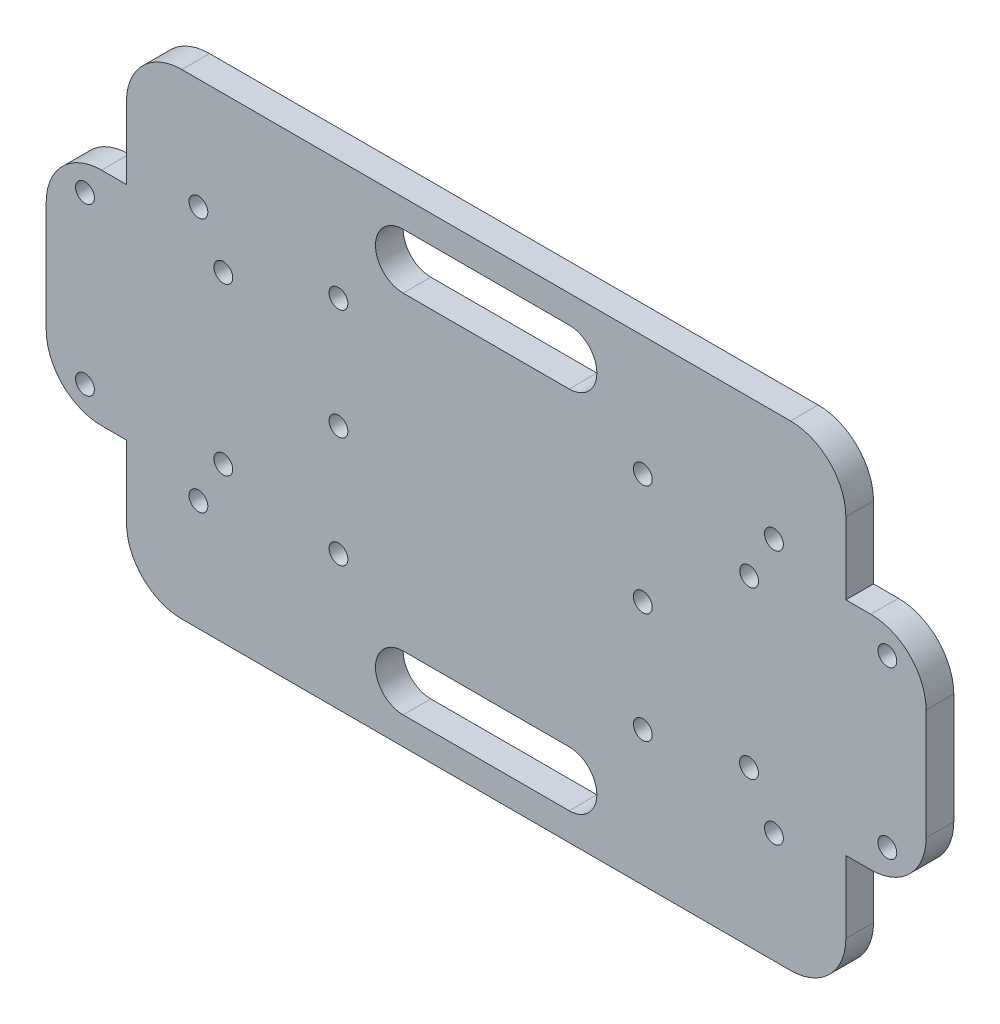
SolidWorks part; units mm, degrees
ref_plane "Front Plane" through (0, 0, 0) normal (0, 0, 1) x (1, 0, 0)
ref_plane "Top Plane" through (0, 0, 0) normal (0, 1, 0) x (1, 0, 0)
ref_plane "Right Plane" through (0, 0, 0) normal (1, 0, 0) x (0, 0, -1)
sketch "Sketch1" plane through (0, 0, 0) normal (0, 0, 1) x (1, 0, 0)
  line L0 (-65, -20) -> (-65, -33)
  line L1 (55, 43) -> (-55, 43)
  line L2 (65, 33) -> (65, 20)
  line L3 (55, -43) -> (-55, -43)
  line L4 (-65, 33) -> (-65, 20)
  line L5 (65, 43) -> (-65, -43) construction
  line L6 (65, -43) -> (-65, 43) construction
  line L7 (-65, 20) -> (-69.5, 20)
  line L9 (-65, -20) -> (-69.5, -20)
  line L10 (-79.5, 10) -> (-79.5, -10)
  line L11 (-65, 0) -> (-79.5, -20) construction
  line L12 (-65, 0) -> (-79.5, 20) construction
  line L13 (65, 20) -> (69.5, 20)
  line L15 (65, -20) -> (69.5, -20)
  line L16 (79.5, 10) -> (79.5, -10)
  line L17 (65, 0) -> (79.5, -20) construction
  line L18 (65, 0) -> (79.5, 20) construction
  line L19 (65, -20) -> (65, -33)
  arc A0 (-65, 33) -> (-55, 43) centre (-55, 33) cw
  arc A1 (-55, -43) -> (-65, -33) centre (-55, -33) cw
  arc A2 (55, -43) -> (65, -33) centre (55, -33) ccw
  arc A3 (65, 33) -> (55, 43) centre (55, 33) ccw
  arc A4 (-79.5, 10) -> (-69.5, 20) centre (-69.5, 10) cw
  arc A5 (-69.5, -20) -> (-79.5, -10) centre (-69.5, -10) cw
  arc A6 (79.5, 10) -> (69.5, 20) centre (69.5, 10) ccw
  arc A7 (69.5, -20) -> (79.5, -10) centre (69.5, -10) ccw
  point P0 (0, 0)
  point P18 (-65, 0)
  point P29 (65, 0)
  dimension "D3" = 10
  dimension "D4" = 10
  dimension "D5" = 10
  dimension "D6" = 10
  dimension "D8" = 10
  dimension "D9" = 10
  dimension "D11" = 10
  dimension "D12" = 10
  dimension "D1" = 130
  dimension "D2" = 86
  dimension "D7" = 40
  dimension "D10" = 40
extrude "Boss-Extrude2" add sketch "Sketch1" along normal blind 5
sketch "Sketch3" plane through (0, 0, 5) normal (0, 0, 1) x (1, 0, 0)
  line L0 (-79.5, 0) -> (-40.5, 0)
  line L1 (-79.5, 10) -> (-79.5, -10) construction
  line L2 (-40.5, 0) -> (-40.5, -20)
  line L3 (-40.5, -20) -> (-47.5, -20)
  line L4 (-47.5, -20) -> (-47.5, -15)
  line L5 (-40.5, 0) -> (-40.5, 20)
  line L6 (-40.5, 20) -> (-47.5, 20)
  line L7 (-47.5, 20) -> (-47.5, 15)
  line L8 (-47.5, -15) -> (-72.5, -15) construction
  line L9 (-47.5, 15) -> (-72.5, 15) construction
  line L10 (79.5, 0) -> (40.5, 0)
  line L11 (79.5, -10) -> (79.5, 10) construction
  line L12 (40.5, 0) -> (40.5, 20)
  line L13 (40.5, 20) -> (47.5237, 20)
  line L14 (47.5237, 20) -> (47.5237, 16.7)
  line L15 (40.5, 0) -> (40.5, -20)
  line L16 (40.5, -20) -> (47.5, -20)
  line L17 (47.5, -20) -> (47.5, -15)
  line L18 (47.5, -15) -> (72.5, -15)
  line L19 (49.2237, 15) -> (72.5, 15)
  line L20 (0, 43) -> (0, 33) construction
  line L21 (-39.1929, 31.3543) -> (-26.6929, 31.3543)
  line L25 (-39.1929, 31.3543) -> (39.1929, -31.3543) construction
  line L26 (-39.1929, -31.3543) -> (39.1929, 31.3543) construction
  line L27 (-26.6929, 31.3543) -> (-26.6929, 21.3543) construction
  line L28 (-26.6929, 21.3543) -> (-26.6929, 1.3543) construction
  line L29 (-26.6929, 1.3543) -> (-26.6929, -18.6457) construction
  line L30 (-26.6929, -18.6457) -> (28.3071, -18.6457) construction
  line L31 (28.3071, -18.6457) -> (28.3071, 1.3543) construction
  line L32 (28.3071, 1.3543) -> (28.3071, 21.3543) construction
  line L33 (47.5237, 43) -> (47.5237, 23) construction
  line L34 (55, 43) -> (-55, 43) construction
  line L35 (65, 23) -> (52, 23) construction
  line L37 (47.5, -43) -> (47.5, -23) construction
  line L38 (-55, -43) -> (55, -43) construction
  line L39 (65, -23) -> (52, -23) construction
  line L41 (-47.5, -43) -> (-47.5, -23) construction
  line L42 (-65, -23) -> (-52, -23) construction
  line L43 (65, -33) -> (65, -20) construction
  line L44 (-47.5, 43) -> (-47.5, 23) construction
  line L45 (-65, 23) -> (-52, 23) construction
  line L46 (-65, -20) -> (-65, -33) construction
  line L47 (-15, 33) -> (15, 33) construction
  line L48 (-15, 38) -> (15, 38)
  line L49 (-15, 28) -> (15, 28)
  line L50 (0, -43) -> (0, -33) construction
  line L51 (-15, -33) -> (15, -33) construction
  line L52 (-65, 33) -> (-65, 20) construction
  line L53 (-15, -28) -> (15, -28)
  line L54 (-15, -38) -> (15, -38)
  line L55 (65, 20) -> (65, 33) construction
  circle A0 centre (-47.5, 15) radius 1.7
  circle A1 centre (-47.5, -15) radius 1.7
  circle A2 centre (-72.5, -15) radius 1.7
  circle A3 centre (-72.5, 15) radius 1.7
  circle A4 centre (47.5237, 15) radius 1.7
  circle A5 centre (47.5, -15) radius 1.7
  circle A6 centre (72.5, 15) radius 1.7
  circle A7 centre (72.5, -15) radius 1.7
  circle A8 centre (-26.6929, 21.3543) radius 1.7
  circle A9 centre (-26.6929, 1.3543) radius 1.7
  circle A10 centre (-26.6929, -18.6457) radius 1.7
  circle A11 centre (28.3071, -18.6457) radius 1.7
  circle A12 centre (28.3071, 1.3543) radius 1.7
  circle A13 centre (28.3071, 21.3543) radius 1.7
  arc A17 (-15, 38) -> (-15, 28) centre (-15, 33) ccw
  arc A18 (15, 28) -> (15, 38) centre (15, 33) ccw
  arc A19 (-15, -28) -> (-15, -38) centre (-15, -33) ccw
  arc A20 (15, -38) -> (15, -28) centre (15, -33) ccw
  circle A22 centre (-52, 23) radius 1.7
  circle A23 centre (-52, -23) radius 1.7
  circle A24 centre (52, -23) radius 1.7
  circle A25 centre (52, 23) radius 1.7
  point P34 (0, 0)
  point P81 (0, 33)
  point P94 (0, -33)
  dimension "D1" = 55
  dimension "D2" = 20
  dimension "D3" = 20
  dimension "D7" = 30
extrude "Cut-Extrude1" cut sketch "Sketch3" against normal blind 5
